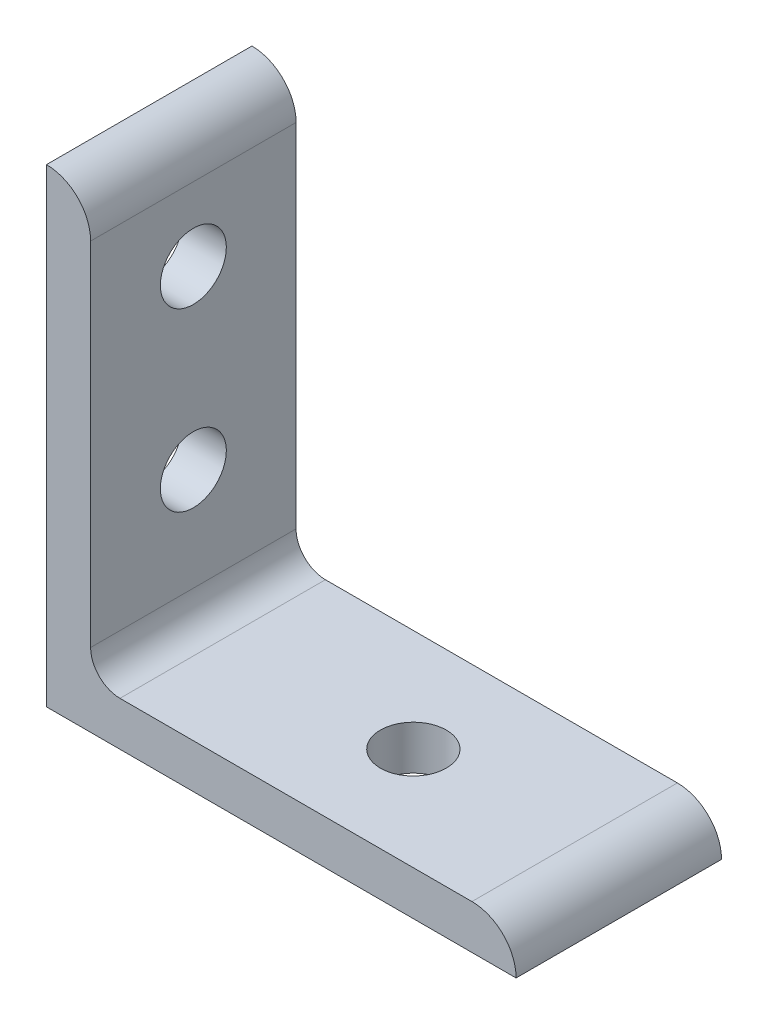
SolidWorks part; units mm, degrees
ref_plane "Front Plane" through (0, 0, 0) normal (0, 0, 1) x (1, 0, 0)
ref_plane "Top Plane" through (0, 0, 0) normal (0, 1, 0) x (1, 0, 0)
ref_plane "Right Plane" through (0, 0, 0) normal (1, 0, 0) x (0, 0, -1)
sketch "Sketch1" plane through (0, 0, 0) normal (0, 0, 1) x (1, 0, 0)
  line L0 (0, 0) -> (0, 50.8)
  line L1 (4.7752, 46.0248) -> (4.7752, 50.8) construction
  line L2 (4.7752, 46.0248) -> (4.7752, 7.9502)
  line L3 (7.9502, 4.7752) -> (46.0248, 4.7752)
  line L4 (4.7752, 50.8) -> (0, 50.8) construction
  line L5 (50.8, 0) -> (0, 0)
  line L6 (46.0248, 4.7752) -> (50.8, 4.7752) construction
  line L7 (50.8, 4.7752) -> (50.8, 0) construction
  arc A0 (4.7752, 46.0248) -> (0, 50.8) centre (0, 46.0248) ccw
  arc A1 (50.8, 0) -> (46.0248, 4.7752) centre (46.0248, 0) ccw
  arc A2 (4.7752, 7.9502) -> (7.9502, 4.7752) centre (7.9502, 7.9502) ccw
  point P10 (4.7752, 48.4124)
  dimension "E" = 3.175
  dimension "D" = 4.7752
  dimension "C" = 50.8
  dimension "B" = 50.8
extrude "Boss-Extrude1" add sketch "Sketch1" along normal mid plane 22.225
sketch "Sketch2" plane through (0, 0, 0) normal (0, 1, 0) x (1, 0, 0)
  line L0 (0, 0) -> (28.575, 0) construction
  circle A0 centre (28.575, 0) radius 3.5687
extrude "Cut-Extrude1" cut sketch "Sketch2" along normal through all
sketch "Sketch3" plane through (0, 0, 0) normal (1, 0, 0) x (0, 0, -1)
  line L0 (0, 0) -> (0, 19.05) construction
  line L1 (0, 19.05) -> (0, 38.1) construction
  circle A0 centre (0, 19.05) radius 3.5687
  circle A1 centre (0, 38.1) radius 3.5687
  dimension "D1" = 19.05
  dimension "D2" = 19.05
extrude "Cut-Extrude2" cut sketch "Sketch3" along normal through all
equation "\"E@Sketch3\" = \"E@Sketch2\""
